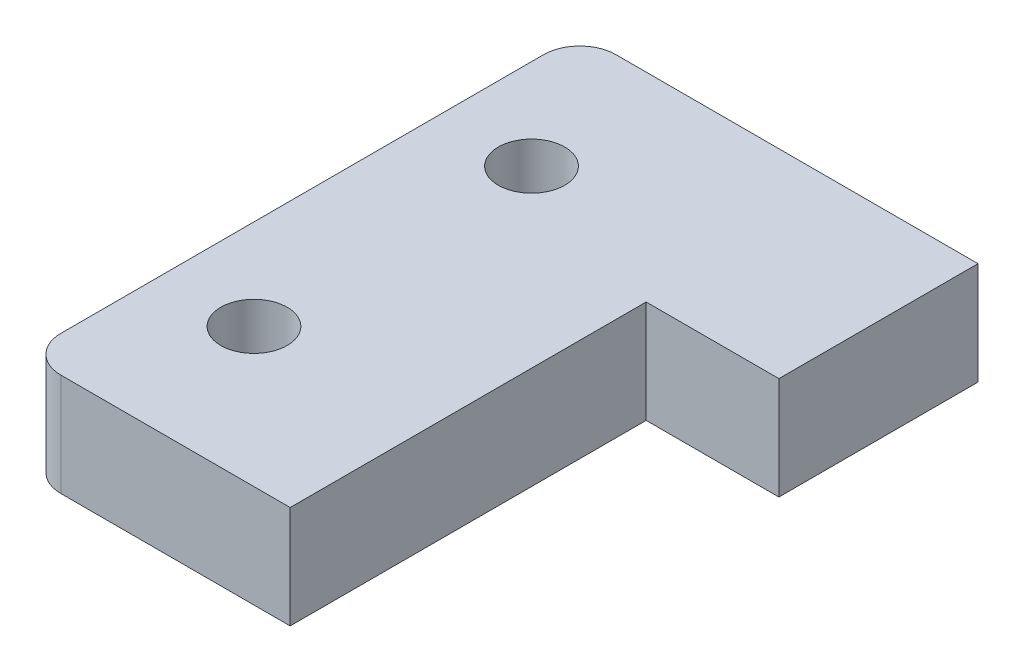
SolidWorks part; units mm, degrees
ref_plane "Plano frontal" through (0, 0, 0) normal (0, 0, 1) x (1, 0, 0)
ref_plane "Plano superior" through (0, 0, 0) normal (0, 1, 0) x (1, 0, 0)
ref_plane "Plano direito" through (0, 0, 0) normal (1, 0, 0) x (0, 0, -1)
sketch "Esboço3" plane through (0, 0, 0) normal (0, 1, 0) x (1, 0, 0)
  line L0 (-16.5, 20) -> (-16.5, -20)
  line L1 (-13.5, -23) -> (5.5, -23)
  line L2 (5.5, -23) -> (5.5, 6.5)
  line L3 (5.5, 6.5) -> (16.5, 6.5)
  line L4 (16.5, 6.5) -> (16.5, 23)
  line L5 (16.5, 23) -> (-13.5, 23)
  arc A0 (-16.5, -20) -> (-13.5, -23) centre (-13.5, -20) ccw
  arc A1 (-13.5, 23) -> (-16.5, 20) centre (-13.5, 20) ccw
  circle A2 centre (-9, 11.5) radius 2.75
  circle A3 centre (-9, -11.5) radius 2.75
extrude "Ressalto-extrusão1" add sketch "Esboço3" along normal blind 8.5
